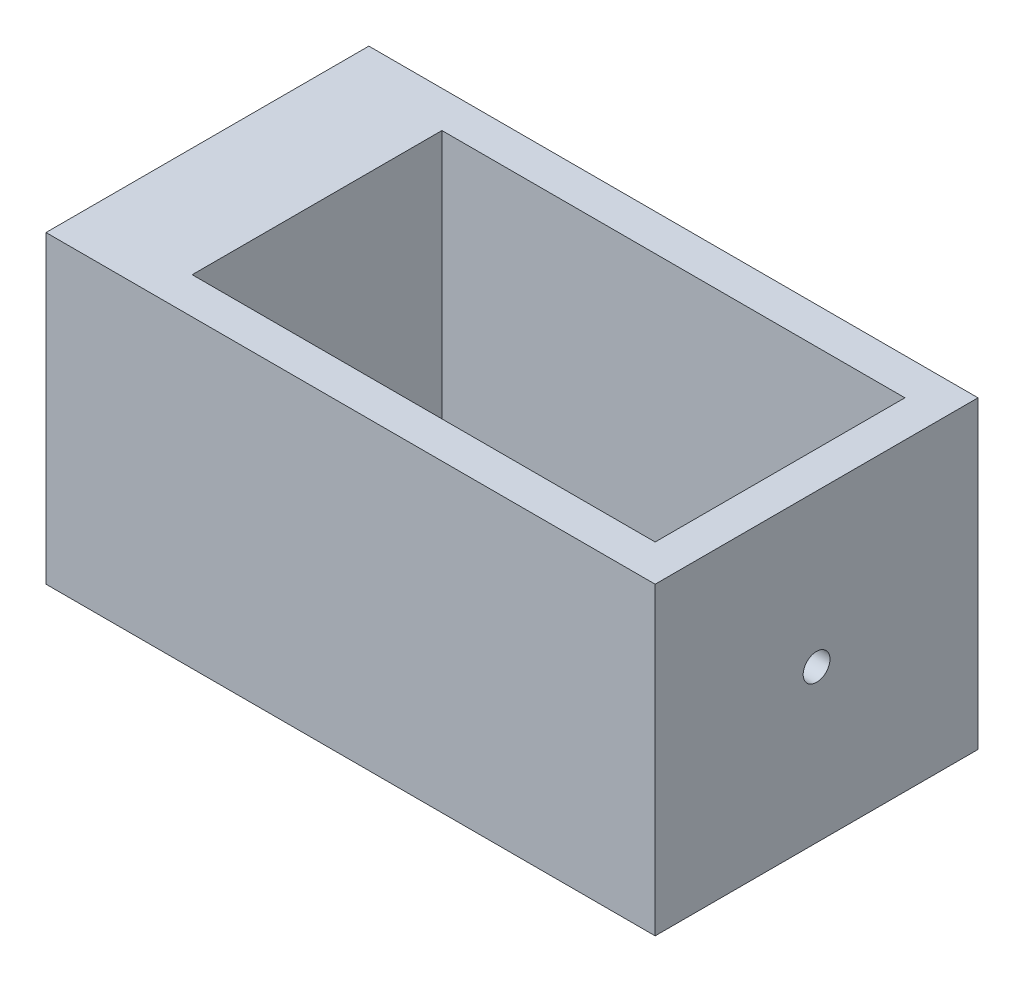
SolidWorks part; units mm, degrees
ref_plane "前视基准面" through (0, 0, 0) normal (0, 0, 1) x (1, 0, 0)
ref_plane "上视基准面" through (0, 0, 0) normal (0, 1, 0) x (1, 0, 0)
ref_plane "右视基准面" through (0, 0, 0) normal (1, 0, 0) x (0, 0, -1)
sketch "草图2" plane through (0, 0, 0) normal (0, 1, 0) x (1, 0, 0)
  line L0 (-38, -26.5) -> (44, -26.5)
  line L1 (-38, 20.5) -> (38, 20.5)
  line L2 (-38, 20.5) -> (-38, -20.5)
  line L3 (-38, -20.5) -> (38, -20.5)
  line L4 (38, 20.5) -> (38, -20.5)
  line L5 (0, -20.5) -> (0, 20.5) construction
  line L6 (-38, 0) -> (38, 0) construction
  line L7 (44, 26.5) -> (44, -26.5)
  line L8 (-38, 26.5) -> (44, 26.5)
  line L9 (-56, 26.5) -> (-56, -26.5)
  line L10 (-56, 26.5) -> (-38, 26.5)
  line L11 (-56, -26.5) -> (-38, -26.5)
  point P0 (0, 0)
  dimension "D1" = 76
  dimension "D2" = 41
  dimension "D3" = 6
  dimension "D4" = 100
extrude "凸台-拉伸1" add sketch "草图2" along normal blind 50
sketch "草图3" plane through (44, 0, 0) normal (1, 0, 0) x (0, 0, -1)
  line L0 (-26.5, 25) -> (26.5, 25) construction
  line L1 (-26.5, 50) -> (-26.5, 0) construction
  line L2 (26.5, 50) -> (26.5, 0) construction
  circle A0 centre (0, 25) radius 2.2
  dimension "D1" = 4.4
extrude "切除-拉伸1" cut sketch "草图3" against normal up to next
